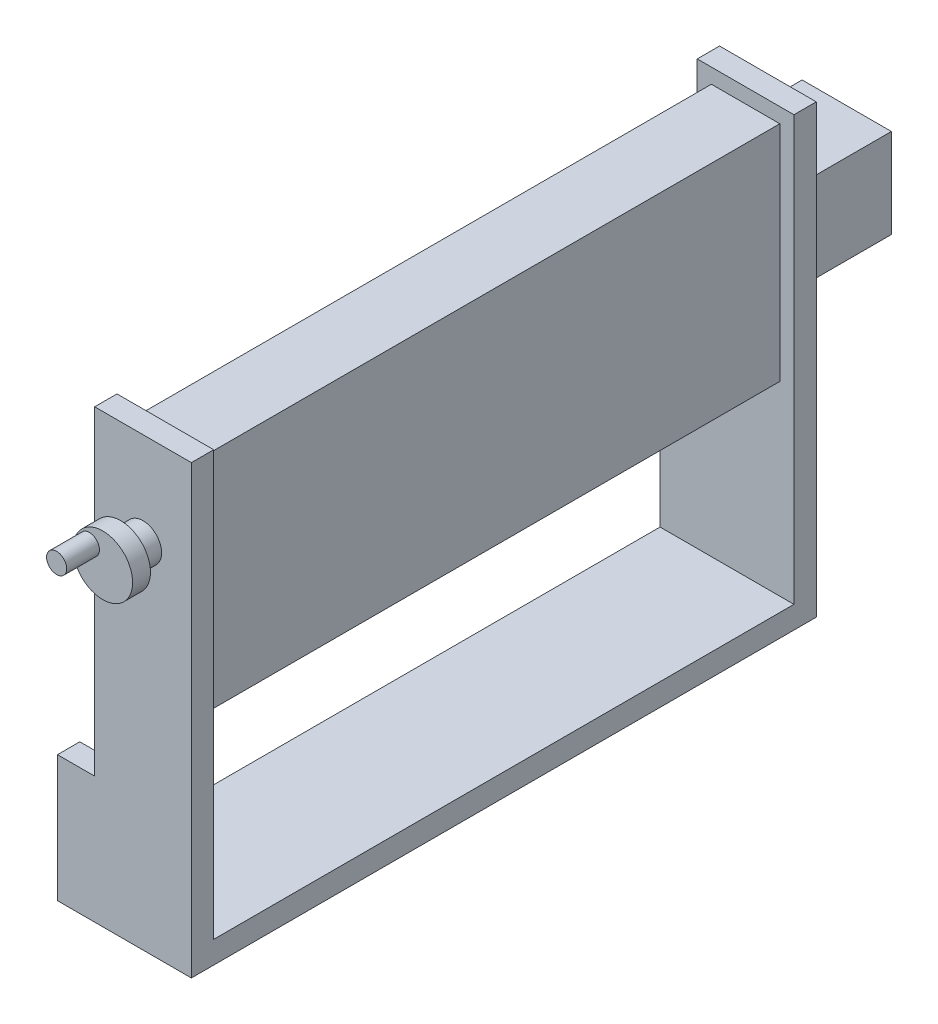
SolidWorks part; units mm, degrees
ref_plane "正面" through (0, 0, 0) normal (0, 0, 1) x (1, 0, 0)
ref_plane "平面" through (0, 0, 0) normal (0, 1, 0) x (1, 0, 0)
ref_plane "右側面" through (0, 0, 0) normal (1, 0, 0) x (0, 0, -1)
sketch "ｽｹｯﾁ1" plane through (0, 0, 0) normal (0, 0, 1) x (1, 0, 0)
  line L1 (0, 0) -> (90, 0)
  line L2 (0, 0) -> (0, 85)
  line L3 (25, 300) -> (90, 300)
  line L4 (90, 0) -> (90, 300)
  line L7 (0, 85) -> (25, 85)
  line L8 (25, 300) -> (25, 85)
  dimension "D1" = 300
  dimension "D2" = 65
  dimension "D3" = 90
  dimension "D4" = 85
extrude "ﾎﾞｽ - 押し出し1" add sketch "ｽｹｯﾁ1" along normal blind 15
sketch "ｽｹｯﾁ2" plane through (0, 0, 15) normal (0, 0, 1) x (1, 0, 0)
  line L0 (57.5, 300) -> (57.5, 0) construction
  line L1 (90, 300) -> (25, 300) construction
  line L2 (0, 0) -> (90, 0) construction
  circle A0 centre (57.5, 237.4626) radius 12.5
  dimension "D1" = 25
extrude "ﾎﾞｽ - 押し出し2" add sketch "ｽｹｯﾁ2" along normal blind 15
sketch "ｽｹｯﾁ3" plane through (0, 0, 30) normal (0, 0, 1) x (1, 0, 0)
  circle A0 centre (57.5, 237.4626) radius 20
  dimension "D1" = 40
extrude "ﾎﾞｽ - 押し出し3" add sketch "ｽｹｯﾁ3" along normal blind 12
sketch "ｽｹｯﾁ4" plane through (0, 0, 0) normal (0, 0, -1) x (-1, 0, 0)
  line L0 (-57.5, 300) -> (-57.5, 0) construction
  line L1 (-90, 300) -> (-25, 300) construction
  line L2 (0, 0) -> (-90, 0) construction
  line L3 (-80.5, 220.1224) -> (-57.5, 220.1224) construction
  line L4 (-80.5, 290) -> (-34.5, 290)
  line L5 (-80.5, 290) -> (-80.5, 140)
  line L6 (-80.5, 140) -> (-34.5, 140)
  line L7 (-34.5, 290) -> (-34.5, 140)
  line L8 (-57.5, 220.1224) -> (-34.5, 220.1224) construction
  dimension "D1" = 23
  dimension "D2" = 150
  dimension "D3" = 10
extrude "ﾎﾞｽ - 押し出し4" add sketch "ｽｹｯﾁ4" along normal blind 390
sketch "ｽｹｯﾁ6" plane through (0, 0, -390) normal (0, 0, -1) x (-1, 0, 0)
  line L1 (-90, 300) -> (-25, 300)
  line L2 (-90, 300) -> (-90, 0)
  line L3 (-90, 0) -> (0, 0)
  line L4 (0, 85) -> (0, 0)
  line L6 (-25, 300) -> (-25, 85)
  line L7 (-25, 85) -> (0, 85)
extrude "ﾎﾞｽ - 押し出し5" add sketch "ｽｹｯﾁ6" along normal blind 15
sketch "ｽｹｯﾁ7" plane through (0, 0, -405) normal (0, 0, -1) x (-1, 0, 0)
  line L0 (-57.5, 300) -> (-57.5, 0) construction
  line L1 (-25, 300) -> (-90, 300) construction
  line L2 (-90, 0) -> (0, 0) construction
  line L3 (-87.5, 192.8275) -> (-57.5, 192.8275) construction
  line L4 (-87.5, 255) -> (-27.5, 255)
  line L5 (-87.5, 255) -> (-87.5, 195)
  line L6 (-87.5, 195) -> (-27.5, 195)
  line L7 (-27.5, 255) -> (-27.5, 195)
  line L8 (-57.5, 192.8275) -> (-27.5, 192.8275) construction
  dimension "D1" = 60
  dimension "D2" = 60
  dimension "D3" = 45
extrude "ﾎﾞｽ - 押し出し6" add sketch "ｽｹｯﾁ7" along normal blind 53
sketch "ｽｹｯﾁ8" plane through (0, 0, -390) normal (0, 0, 1) x (1, 0, 0)
  line L0 (0, 0) -> (0, 85) construction
  line L1 (0, 15) -> (90, 15)
  line L2 (0, 15) -> (0, 0)
  line L3 (0, 0) -> (90, 0)
  line L4 (90, 15) -> (90, 0)
  dimension "D1" = 15
extrude "ﾎﾞｽ - 押し出し7" add sketch "ｽｹｯﾁ8" along normal up to next
sketch "ｽｹｯﾁ9" plane through (0, 0, 42) normal (0, 0, 1) x (1, 0, 0)
  circle A0 centre (48.4435, 245.3089) radius 6.7581
extrude "ﾎﾞｽ - 押し出し8" add sketch "ｽｹｯﾁ9" along normal blind 22
